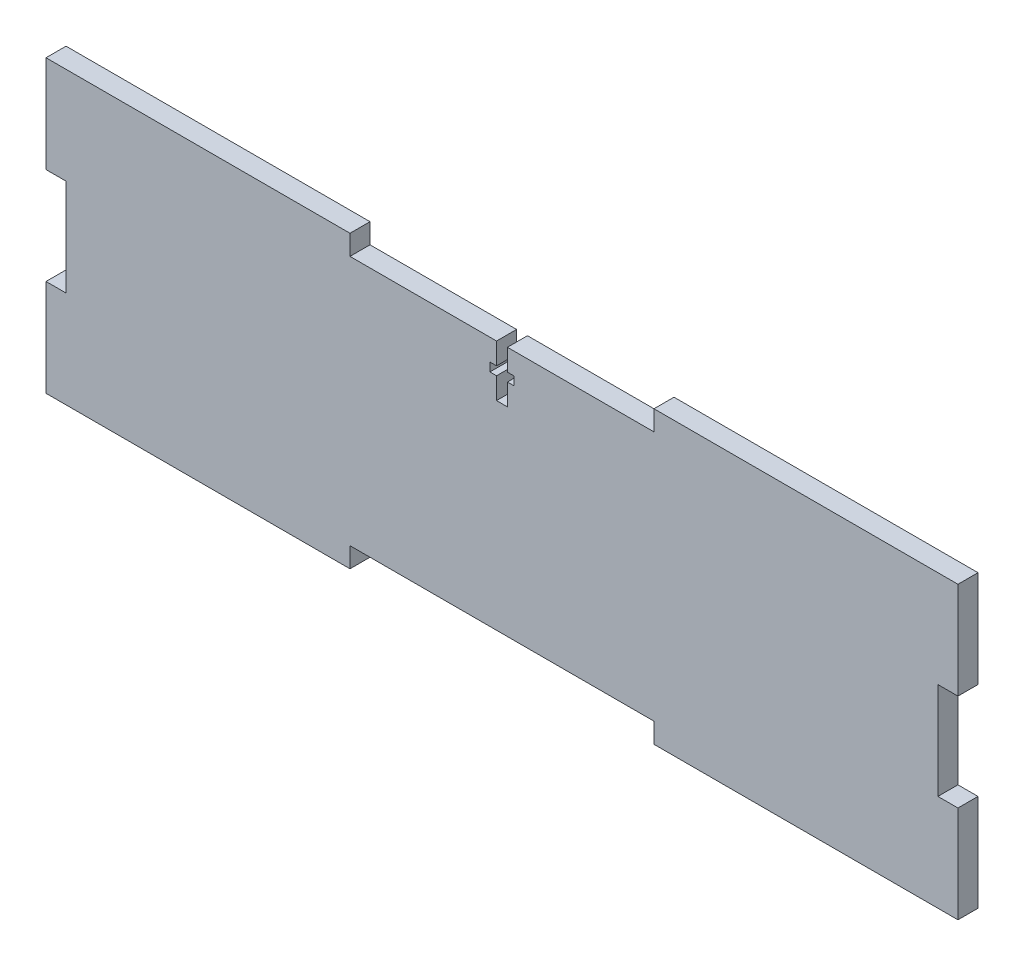
SolidWorks part; units mm, degrees
ref_plane "Front Plane" through (0, 0, 0) normal (0, 0, 1) x (1, 0, 0)
ref_plane "Top Plane" through (0, 0, 0) normal (0, 1, 0) x (1, 0, 0)
ref_plane "Right Plane" through (0, 0, 0) normal (1, 0, 0) x (0, 0, -1)
sketch "Sketch1" plane through (0, 0, 0) normal (0, 0, 1) x (1, 0, 0)
  line L1 (-115.57, -36.83) -> (115.57, -36.83)
  line L2 (-115.57, -36.83) -> (-115.57, 36.83)
  line L3 (-115.57, 36.83) -> (115.57, 36.83)
  line L4 (115.57, -36.83) -> (115.57, 36.83)
  line L5 (-115.57, -36.83) -> (115.57, 36.83) construction
  line L6 (-115.57, 36.83) -> (115.57, -36.83) construction
  point P0 (0, 0)
  dimension "D1" = 231.14
  dimension "D2" = 73.66
extrude "Boss-Extrude1" add sketch "Sketch1" along normal blind 5.08
sketch "Sketch2" plane through (0, 0, 5.08) normal (0, 0, 1) x (1, 0, 0)
  line L0 (38.5233, -36.83) -> (38.5233, -31.75)
  line L1 (-38.5233, 36.83) -> (38.5233, 36.83)
  line L2 (-38.5233, 36.83) -> (-38.5233, 31.75)
  line L3 (-38.5233, 31.75) -> (38.5233, 31.75)
  line L4 (38.5233, 36.83) -> (38.5233, 31.75)
  line L5 (115.57, 36.83) -> (-115.57, 36.83) construction
  line L6 (0, 0) -> (115.57, 0) construction
  line L7 (115.57, -36.83) -> (115.57, 36.83) construction
  line L8 (-38.5233, -36.83) -> (38.5233, -36.83)
  line L9 (-38.5233, -36.83) -> (-38.5233, -31.75)
  line L10 (-38.5233, -31.75) -> (38.5233, -31.75)
  dimension "D1" = 77.0467
  dimension "D2" = 5.08
  dimension "D3" = 77.0467
extrude "Cut-Extrude1" cut sketch "Sketch2" against normal through all
sketch "Sketch3" plane through (0, 0, 5.08) normal (0, 0, 1) x (1, 0, 0)
  line L0 (-115.57, 36.83) -> (-115.57, -36.83) construction
  line L1 (-115.57, 12.2767) -> (-110.49, 12.2767)
  line L2 (-115.57, 12.2767) -> (-115.57, -12.2767)
  line L3 (-115.57, -12.2767) -> (-110.49, -12.2767)
  line L4 (-110.49, 12.2767) -> (-110.49, -12.2767)
  line L5 (0, 0) -> (0, 39.951) construction
  line L6 (115.57, -12.2767) -> (110.49, -12.2767)
  line L7 (115.57, 12.2767) -> (115.57, -12.2767)
  line L8 (115.57, 12.2767) -> (110.49, 12.2767)
  line L9 (110.49, 12.2767) -> (110.49, -12.2767)
  dimension "D1" = 5.08
  dimension "D2" = 24.5533
  dimension "D3" = 24.5533
extrude "Cut-Extrude2" cut sketch "Sketch3" against normal through all
sketch "Sketch5" plane through (0, 0, 5.08) normal (0, 0, 1) x (1, 0, 0)
  line L0 (0, 0) -> (0, 31.75) construction
  line L1 (-38.5233, 31.75) -> (38.5233, 31.75) construction
  line L2 (0, 0) -> (35.9654, 0) construction
  line L3 (1.378, 31.75) -> (-1.378, 31.75)
  line L4 (1.378, 31.75) -> (1.378, 18.669)
  line L5 (1.378, 18.669) -> (-1.3779, 18.669)
  line L6 (-1.378, 31.75) -> (-1.3779, 18.669)
  dimension "D1" = 1.378
  dimension "D2" = 1.378
  dimension "D3" = 13.081
extrude "Cut-Extrude4" cut sketch "Sketch5" against normal through all
sketch "Sketch6" plane through (0, 0, 5.08) normal (0, 0, 1) x (1, 0, 0)
  line L3 (1.3779, 25.2095) -> (-1.3779, 25.2095) construction
  line L4 (1.378, 31.75) -> (1.378, 18.669) construction
  line L5 (-1.3779, 18.669) -> (-1.378, 31.75) construction
  line L6 (1.3779, 25.2095) -> (-3.048, 25.2095) construction
  line L7 (-3.048, 26.2954) -> (3.048, 26.2954)
  line L8 (-3.048, 26.2954) -> (-3.048, 24.1237)
  line L9 (-3.048, 24.1237) -> (3.048, 24.1237)
  line L10 (3.048, 26.2954) -> (3.048, 24.1237)
  line L11 (0, 0) -> (19.2929, 0) construction
  line L12 (0, 0) -> (0, 14.5303) construction
  line L22 (0, 18.669) -> (0, 24.1237) construction
  line L23 (1.378, 18.669) -> (-1.3779, 18.669) construction
  dimension "D1" = 6.096
  dimension "D2" = 2.1717
extrude "Cut-Extrude5" cut sketch "Sketch6" against normal through all
equation "\"Length\"= \"Length@Box.SLDASM\""
equation "\"D1@Sketch1\"  = \"Length\" + 2 * \"Material\""
equation "\"Width\"= \"Height@Box.SLDASM\""
equation "\"D2@Sketch1\" = \"Width\" + 2 * \"Material\""
equation "\"Material\"= \"Material@Box.SLDASM\""
equation "\"D1@Boss-Extrude1\" = \"Material\""
equation "\"D1@Sketch2\"=(\"Length\" +\"Material\"*2)/3"
equation "\"D2@Sketch2\"= \"Material\""
equation "\"D3@Sketch2\"=(\"Length\" +\"Material\"*2)/3"
equation "\"D1@Sketch3\"=\"Material\""
equation "\"D2@Sketch3\"=(\"Width\" +\"Material\"*2)/3"
equation "\"D3@Sketch3\"=(\"Width\" +\"Material\"*2)/3"
equation "\"Diameter of Screw\"= \"Diameter of Screw@Box.SLDASM\""
equation "\"Length of screw\"= \"Length of Screw@Box.SLDASM\""
equation "\"D3@Sketch5\"=\"Length of screw\" - \"Material\""
equation "\"D2@Sketch5\"=\"Diameter of Screw\"/2"
equation "\"D1@Sketch5\"= \"Diameter of Screw\" /2"
equation "\"Diameter of Nut\"= \"Diameter of Nut@Box.SLDASM\""
equation "\"D1@Sketch6\"=\"Diameter of Nut\""
equation "\"Height of Nut\"= \"Height of Nut@Box.SLDASM\""
equation "\"D2@Sketch6\"=\"Height of Nut\""
